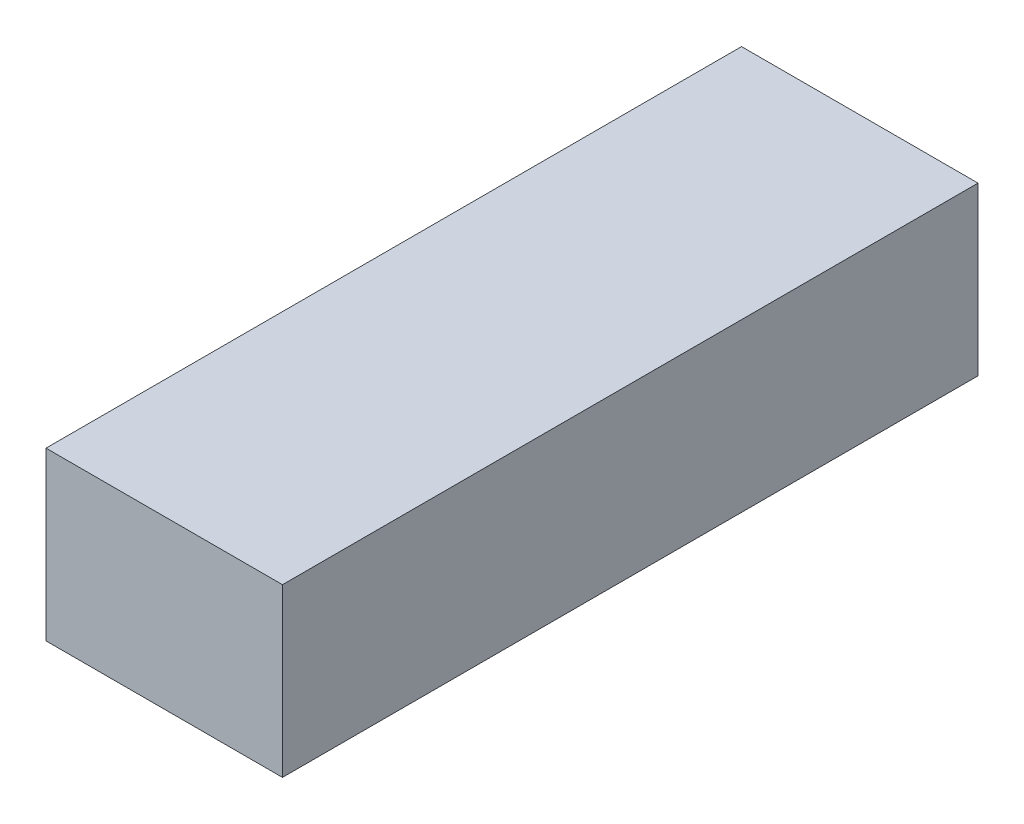
SolidWorks part; units mm, degrees
ref_plane "Front Plane" through (0, 0, 0) normal (0, 0, 1) x (1, 0, 0)
ref_plane "Top Plane" through (0, 0, 0) normal (0, 1, 0) x (1, 0, 0)
ref_plane "Right Plane" through (0, 0, 0) normal (1, 0, 0) x (0, 0, -1)
sketch "Sketch1" plane through (0, 0, 0) normal (0, 1, 0) x (1, 0, 0)
  line L0 (0, 17.3235) -> (0, -20.7882) construction
  line L1 (-3.95, 3.95) -> (3.95, 3.95)
  line L2 (-3.95, 3.95) -> (-3.95, -3.95)
  line L3 (-3.95, -3.95) -> (3.95, -3.95)
  line L4 (3.95, 3.95) -> (3.95, -3.95)
  line L5 (-3.95, 3.95) -> (3.95, -3.95) construction
  line L6 (-3.95, -3.95) -> (3.95, 3.95) construction
  line L7 (3.95, -3.95) -> (5.95, -3.95) construction
  line L8 (-5.95, 26.65) -> (5.95, 26.65)
  line L9 (-5.95, 26.65) -> (-5.95, -8.35)
  line L10 (-5.95, -8.35) -> (5.95, -8.35)
  line L11 (5.95, 26.65) -> (5.95, -8.35)
  line L12 (-5.95, 26.65) -> (5.95, -8.35) construction
  line L13 (-5.95, -8.35) -> (5.95, 26.65) construction
  point P0 (0, 0)
  point P7 (0, 9.15)
  dimension "D1" = 7.9
  dimension "D2" = 2
  dimension "D3" = 4.4
  dimension "D4" = 35
extrude "Boss-Extrude1" add sketch "Sketch1" along normal blind 2.8
sketch "Sketch2" plane through (0, 2.8, 0) normal (0, 1, 0) x (1, 0, 0)
  line L0 (-3.95, 3.95) -> (-3.95, -3.95) construction
  line L1 (-3.45, -3.45) -> (3.45, -3.45)
  line L2 (-3.45, -3.45) -> (-3.45, 3.45)
  line L3 (-3.45, 3.45) -> (3.45, 3.45)
  line L4 (5.95, -8.35) -> (5.95, 26.65)
  line L5 (5.95, 26.65) -> (-5.95, 26.65)
  line L6 (-5.95, 26.65) -> (-5.95, -8.35)
  line L7 (-5.95, -8.35) -> (5.95, -8.35)
  line L8 (5.95, -8.35) -> (5.95, 26.65)
  line L9 (5.95, 26.65) -> (-5.95, 26.65)
  line L10 (-5.95, 26.65) -> (-5.95, -8.35)
  line L11 (-5.95, -8.35) -> (5.95, -8.35)
  line L12 (3.45, -3.45) -> (3.45, 3.45)
  line L13 (-3.45, -3.45) -> (3.45, 3.45) construction
  line L14 (-3.45, 3.45) -> (3.45, -3.45) construction
  line L15 (-3.45, 3.45) -> (-3.95, 3.45) construction
  line L16 (-3.45, 3.45) -> (-3.45, 3.95) construction
  line L17 (3.95, 3.95) -> (-3.95, 3.95) construction
  line L18 (0, 26.65) -> (0, -8.35) construction
  line L20 (3.45, 24.65) -> (-3.45, 24.65)
  line L21 (3.45, 24.65) -> (3.45, 3.45)
  line L22 (3.45, 3.45) -> (-3.45, 3.45)
  line L23 (-3.45, 24.65) -> (-3.45, 3.45)
  line L24 (3.45, 24.65) -> (-3.45, 3.45) construction
  line L25 (3.45, 3.45) -> (-3.45, 24.65) construction
  point P2 (0, 0)
  point P18 (0, 14.05)
  line M12 (5.95, -8.35) -> (5.95, 26.65)
  line M13 (5.95, 26.65) -> (-5.95, 26.65)
  line M14 (-5.95, 26.65) -> (-5.95, -8.35)
  line M15 (-5.95, -8.35) -> (5.95, -8.35)
  line M16 (-3.95, 3.95) -> (3.95, 3.95)
  line M17 (3.95, 3.95) -> (3.95, -3.95)
  line M18 (3.95, -3.95) -> (-3.95, -3.95)
  line M19 (-3.95, -3.95) -> (-3.95, 3.95)
  dimension "D2" = 0.5
  dimension "D3" = 2
  dimension "D1" = 0
extrude "Boss-Extrude2" add sketch "Sketch2" along normal blind 4 contours L23 L20 L21 M15 M12 M13 M14 M16 M17 M18 M19 | L23 L21 L12 L1 L2 M16 M19 M18 M17
sketch "Sketch3" plane through (0, 6.8, 0) normal (0, 1, 0) x (1, 0, 0)
  line L4 (-5.95, -8.35) -> (5.95, -8.35)
  line L5 (5.95, -8.35) -> (5.95, 26.65)
  line L6 (5.95, 26.65) -> (-5.95, 26.65)
  line L7 (-5.95, 26.65) -> (-5.95, -8.35)
  line L8 (-5.95, -8.35) -> (5.95, -8.35)
  line L9 (5.95, -8.35) -> (5.95, 26.65)
  line L10 (5.95, 26.65) -> (-5.95, 26.65)
  line L11 (-5.95, 26.65) -> (-5.95, -8.35)
  dimension "D1" = 0
extrude "Boss-Extrude3" add sketch "Sketch3" along normal blind 1.6
ref_plane "Plane1" through (0, -8.5651, -3.1175) normal (0, -0.9397, -0.342) x (-1, 0, 0)
sketch "Sketch4" plane through (0, -8.5651, -3.1175) normal (0, -0.9397, -0.342) x (-1, 0, 0)
  line L0 (0, 25.0428) -> (0, -7.8464) construction
  line L1 (-5.95, 25.0428) -> (5.95, 25.0428) construction
  line L2 (5.95, -7.8464) -> (-5.95, -7.8464) construction
  line L3 (-5.95, 23.0428) -> (5.95, 23.0428) construction
  line L4 (-5.95, -7.8464) -> (-5.95, 25.0428) construction
  line L5 (5.95, 25.0428) -> (5.95, -7.8464) construction
  line L6 (-4.125, 18.9178) -> (4.125, 18.9178) construction
  circle A0 centre (0, 18.9178) radius 4.125
  circle A1 centre (-4.125, 18.9178) radius 0.3
  circle A2 centre (4.125, 18.9178) radius 0.3
  circle A3 centre (0, 14.7928) radius 0.3
  circle A4 centre (0, 23.0428) radius 0.3
  dimension "D1" = 8.25
  dimension "D3" = 0.6
  dimension "D2" = 2
extrude "Cut-Extrude1" cut sketch "Sketch4" against normal blind 7.3 contours A4 A0 A1 A3 A2
chamfer "Chamfer1" distance 1 angle 45 1 edges at (0, 0, 3.95)
equation "\"LedSize\"= 7.6"
equation "\"D1@Sketch1\"=\"LedSize\"+0.3"
